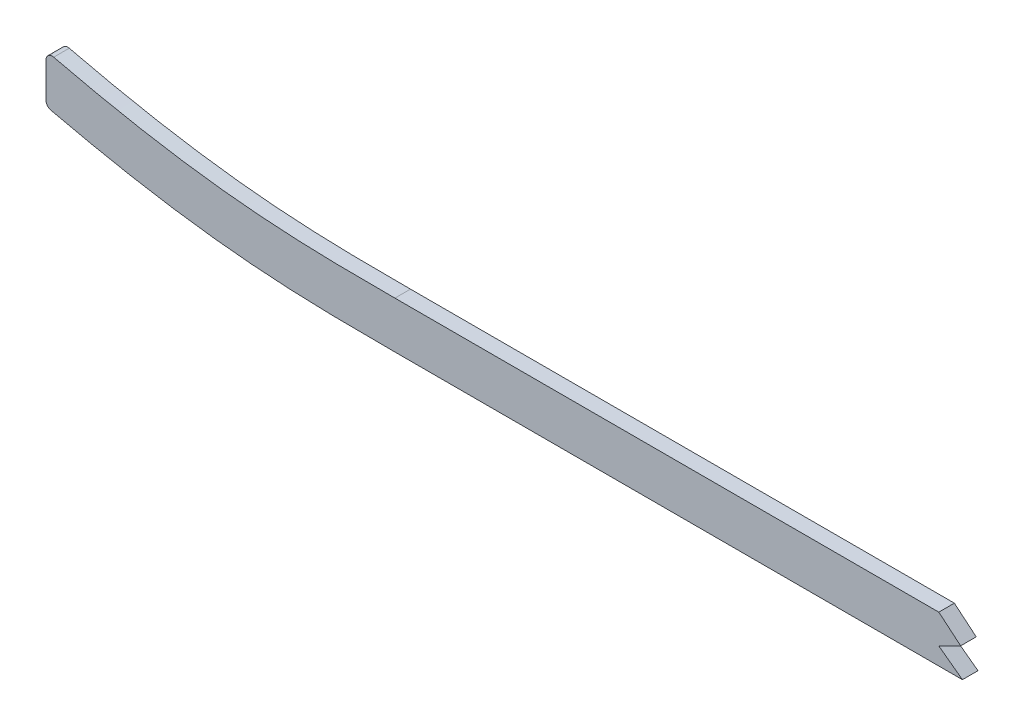
SolidWorks part; units mm, degrees
ref_plane "Front Plane" through (0, 0, 0) normal (0, 0, 1) x (1, 0, 0)
ref_plane "Top Plane" through (0, 0, 0) normal (0, 1, 0) x (1, 0, 0)
ref_plane "Right Plane" through (0, 0, 0) normal (1, 0, 0) x (0, 0, -1)
sketch "Sketch1" plane through (0, 0, 0) normal (0, 0, 1) x (1, 0, 0)
  line L0 (1046.2855, 53.4707) -> (499.61, 53.4707) construction
  line L1 (55, 0) -> (-55, 0) construction
  line L2 (1046.2855, -53.4707) -> (499.61, -53.4707)
  line L3 (1046.2855, -34.4207) -> (499.61, -34.4207)
  line L4 (99.06, -18.1493) -> (99.06, -37.7415)
  line L5 (2669.54, 9.5231) -> (2669.54, -9.569)
  spline S0 degree 5 poles (2699.7923, 7.5245) (2639.6368, 11.6572) (2579.4813, 15.4358) (2518.4981, 19.1485) (2436.3555, 23.2524) (2354.213, 26.6315) (2332.5703, 27.481) (2156.2686, 34.3778) (1979.9669, 41.6286) (1824.1143, 52.7713) (1636.9286, 53.5796) (1449.7429, 53.454) (1418.0067, 53.4707) (1324.8993, 53.4707) (1231.7919, 53.4707) (1170.4413, 53.4707) (1108.7841, 53.4707) (1047.1269, 53.4707) (1046.8464, 53.4707) (1046.5659, 53.4707) (1046.2855, 53.4707) knots 100.654805 100.654805 100.654805 100.654805 100.654805 100.654805 130.927897 130.927897 130.927897 141.337055 141.337055 141.337055 218.101815 218.101815 218.101815 233.772059 233.772059 233.772059 264.077723 264.077723 264.077723 264.216209 264.216209 264.216209 264.216209 264.216209 264.216209 weights 1 1 1 1 1 1 1 1 1 1 1 1 1 1 1 1 1 1 1 1 1 construction
  spline S1 degree 5 poles (499.61, 53.4707) (492.1368, 53.4707) (484.7543, 53.4707) (477.443, 53.4707) (448.5166, 53.4707) (419.5901, 53.4707) (398.3681, 53.4707) (355.6475, 53.4707) (312.927, 53.4707) (289.2351, 53.4703) (265.365, 53.4707) (241.4948, 53.4707) (241.4716, 53.4707) (241.4484, 53.4707) (241.4251, 53.4707) knots 19.90683 19.90683 19.90683 19.90683 19.90683 19.90683 23.637897 23.637897 23.637897 34.276546 34.276546 34.276546 46.401341 46.401341 46.401341 46.413154 46.413154 46.413154 46.413154 46.413154 46.413154 weights 1 1 1 1 1 1 1 1 1 1 1 1 1 1 1 construction
  spline S2 degree 5 poles (241.4251, 53.4707) (224.2869, 53.4707) (207.1495, 53.4673) (190.2039, 52.6866) (151.6561, 49.0319) (113.1083, 41.5037) (91.9499, 36.3426) (71.313, 30.9696) (50.6762, 24.7565) knots 0 0 0 0 0 0 8.713816 8.713816 8.713816 19.90683 19.90683 19.90683 19.90683 19.90683 19.90683 weights 1 1 1 1 1 1 1 1 1 construction
  spline S3 degree 5 poles (241.4251, -53.4707) (224.2869, -53.4707) (207.1495, -53.4673) (190.2039, -52.6866) (151.6561, -49.0319) (113.1083, -41.5037) (91.9499, -36.3426) (71.313, -30.9696) (50.6762, -24.7565) knots 0 0 0 0 0 0 8.713816 8.713816 8.713816 19.90683 19.90683 19.90683 19.90683 19.90683 19.90683 weights 1 1 1 1 1 1 1 1 1
  spline S4 degree 5 poles (499.61, -53.4707) (492.1368, -53.4707) (484.7543, -53.4707) (477.443, -53.4707) (448.5166, -53.4707) (419.5901, -53.4707) (398.3681, -53.4707) (355.6475, -53.4707) (312.927, -53.4707) (289.2351, -53.4703) (265.365, -53.4707) (241.4948, -53.4707) (241.4716, -53.4707) (241.4484, -53.4707) (241.4251, -53.4707) knots 19.90683 19.90683 19.90683 19.90683 19.90683 19.90683 23.637897 23.637897 23.637897 34.276546 34.276546 34.276546 46.401341 46.401341 46.401341 46.413154 46.413154 46.413154 46.413154 46.413154 46.413154 weights 1 1 1 1 1 1 1 1 1 1 1 1 1 1 1
  spline S5 degree 5 poles (2699.7923, -7.5245) (2639.6368, -11.6572) (2579.4813, -15.4358) (2518.4981, -19.1485) (2436.3555, -23.2524) (2354.213, -26.6315) (2332.5703, -27.481) (2156.2686, -34.3778) (1979.9669, -41.6286) (1824.1143, -52.7713) (1636.9286, -53.5796) (1449.7429, -53.454) (1418.0067, -53.4707) (1324.8993, -53.4707) (1231.7919, -53.4707) (1170.4413, -53.4707) (1108.7841, -53.4707) (1047.1269, -53.4707) (1046.8464, -53.4707) (1046.5659, -53.4707) (1046.2855, -53.4707) knots 100.654805 100.654805 100.654805 100.654805 100.654805 100.654805 130.927897 130.927897 130.927897 141.337055 141.337055 141.337055 218.101815 218.101815 218.101815 233.772059 233.772059 233.772059 264.077723 264.077723 264.077723 264.216209 264.216209 264.216209 264.216209 264.216209 264.216209 weights 1 1 1 1 1 1 1 1 1 1 1 1 1 1 1 1 1 1 1 1 1
  spline S6 degree 1 poles (2698.4867, 11.4807) (1046.2855, -34.4207) knots 0 0 1 1 construction
  spline S7 degree 1 poles (499.61, -34.4207) (241.4252, -34.4207) knots 0 0 1 1 construction
  spline S8 degree 1 poles (241.4252, -34.4207) (56.168, -6.5153) knots 0 0 1 1 construction
  spline S9 degree 3 poles (2698.4867, 11.4807) (2691.2474, 10.9833) (2679.1952, 10.1655) (2662.2765, 9.0388) (2635.6663, 7.2925) (2596.8577, 4.8261) (2545.7297, 1.7583) (2494.4053, -1.0986) (2451.533, -3.2666) (2417.1983, -4.8671) (2391.4571, -6.0036) (2365.6347, -7.0869) (2339.5463, -8.1377) (2313.4661, -9.1651) (2287.6124, -10.1795) (2261.7633, -11.201) (2227.2853, -12.5838) (2184.1756, -14.3661) (2132.4291, -16.6074) (2063.4255, -19.7089) (1977.1749, -23.7005) (1873.7325, -28.1494) (1770.3746, -31.6575) (1667.0857, -33.7931) (1581.0111, -34.3832) (1512.074, -34.4278) (1443.0615, -34.4095) (1356.8009, -34.4244) (1218.7946, -34.4185) (1115.289, -34.4207) (1046.2855, -34.4207) knots 100.654805 100.654805 100.654805 100.654805 102.842388 104.300777 105.766098 110.877392 115.988686 121.09998 126.211274 128.766921 131.322568 133.878215 136.433862 138.989509 141.545156 144.100803 146.656449 151.767743 156.879037 161.990331 172.212919 182.435507 192.658094 202.880682 213.10327 218.214564 223.325858 233.548445 243.771033 264.216209 264.216209 264.216209 264.216209
  spline S10 degree 3 poles (499.61, -34.4207) (488.6147, -34.4207) (472.2364, -34.4207) (449.9402, -34.4207) (427.7713, -34.4207) (405.8747, -34.4207) (384.5849, -34.4207) (368.9002, -34.4207) (353.3766, -34.4207) (332.6085, -34.4207) (306.2878, -34.4206) (274.0235, -34.4205) (252.271, -34.4207) (241.4252, -34.4207) knots 19.90683 19.90683 19.90683 19.90683 23.22012 24.876765 26.533411 29.846701 31.503346 33.159992 34.816637 36.473282 39.786573 43.099863 46.413154 46.413154 46.413154 46.413154
  spline S11 degree 3 poles (241.4252, -34.4207) (239.3949, -34.4207) (235.3223, -34.4205) (227.2744, -34.3987) (217.3194, -34.2975) (205.5307, -33.9764) (189.9633, -33.2126) (170.697, -31.5435) (147.5333, -28.3144) (125.4828, -24.2021) (107.4399, -20.1965) (92.2061, -16.4882) (75.9505, -12.2555) (63.6202, -8.7589) (56.168, -6.5153) knots 0 0 0 0 0.622088 1.244177 2.488354 3.732531 4.976707 7.465061 9.953415 12.441768 14.558235 15.802412 17.418476 19.90683 19.90683 19.90683 19.90683
  point P2 (0, 0)
  dimension "D1" = 50.6762
  dimension "D3" = 99.06
  dimension "D4" = 2669.54
  dimension "D2" = 19.05
extrude "Boss-Extrude1" add sketch "Sketch1" along normal mid plane 6.35 contours S10 S11 L4 S3 S4 L2 S5 L5 S9 L3
sketch "Sketch2" plane through (0, 0, 3.175) normal (0, 0, 1) x (1, 0, 0)
  line L0 (2187.01, -14.2633) -> (2312.9875, -14.2633)
  line L1 (2312.9875, -14.2633) -> (2312.9875, -9.1833)
  spline S0 degree 3 poles (689.0175, 232.3189) (4033.8285, 148.9311) (3356.6623, 54.6077) (2635.6663, 7.2925) (2596.8577, 4.8261) (2545.7297, 1.7583) (2494.4053, -1.0986) (2451.533, -3.2666) (2417.1983, -4.8671) (2391.4571, -6.0036) (2365.6347, -7.0869) (2339.5463, -8.1377) (2313.4661, -9.1651) (2287.6124, -10.1795) (2261.7633, -11.201) (2227.2853, -12.5838) (2184.1756, -14.3661) (2132.4291, -16.6074) (2063.4255, -19.7089) (1977.1749, -23.7005) (1873.7325, -28.1494) (1770.3746, -31.6575) (1667.0857, -33.7931) (1581.0111, -34.3832) (1512.074, -34.4278) (1443.0615, -34.4095) (1356.8009, -34.4244) (551.9641, -34.3896) (-218.4198, -34.7282) (-953.6342, -29.9632) knots -106.828462 -106.828462 -106.828462 -106.828462 104.300777 105.766098 110.877392 115.988686 121.09998 126.211274 128.766921 131.322568 133.878215 136.433862 138.989509 141.545156 144.100803 146.656449 151.767743 156.879037 161.990331 172.212919 182.435507 192.658094 202.880682 213.10327 218.214564 223.325858 233.548445 243.771033 461.793666 461.793666 461.793666 461.793666 only from (2669.54, 9.5231) to (1046.2855, -34.4207) construction
  spline S1 degree 3 poles (2669.54, 9.5231) (2667.1265, 9.3624) (2659.8616, 8.8803) (2635.6663, 7.2925) (2596.8577, 4.8261) (2545.7297, 1.7583) (2494.4053, -1.0986) (2451.533, -3.2666) (2417.1983, -4.8671) (2391.4571, -6.0036) (2365.6347, -7.0869) (2339.5463, -8.1377) (2313.4661, -9.1651) (2287.6124, -10.1795) (2261.7633, -11.201) (2227.2853, -12.5838) (2184.1756, -14.3661) (2132.4291, -16.6074) (2063.4255, -19.7089) (1977.1749, -23.7005) (1873.7325, -28.1494) (1770.3746, -31.6575) (1667.0857, -33.7931) (1581.0111, -34.3832) (1512.074, -34.4278) (1443.0615, -34.4095) (1356.8009, -34.4244) (1218.7946, -34.4185) (1115.289, -34.4207) (1046.2855, -34.4207) knots 103.571583 103.571583 103.571583 103.571583 104.300777 105.766098 110.877392 115.988686 121.09998 126.211274 128.766921 131.322568 133.878215 136.433862 138.989509 141.545156 144.100803 146.656449 151.767743 156.879037 161.990331 172.212919 182.435507 192.658094 202.880682 213.10327 218.214564 223.325858 233.548445 243.771033 264.216209 264.216209 264.216209 264.216209
  point P2 (0, 0)
  spline M9 degree 3 poles (2698.4867, 11.4807) (2691.2474, 10.9833) (2679.1952, 10.1655) (2662.2765, 9.0388) (2635.6663, 7.2925) (2596.8577, 4.8261) (2545.7297, 1.7583) (2494.4053, -1.0986) (2451.533, -3.2666) (2417.1983, -4.8671) (2391.4571, -6.0036) (2365.6347, -7.0869) (2339.5463, -8.1377) (2313.4661, -9.1651) (2287.6124, -10.1795) (2261.7633, -11.201) (2227.2853, -12.5838) (2184.1756, -14.3661) (2132.4291, -16.6074) (2063.4255, -19.7089) (1977.1749, -23.7005) (1873.7325, -28.1494) (1770.3746, -31.6575) (1667.0857, -33.7931) (1581.0111, -34.3832) (1512.074, -34.4278) (1443.0615, -34.4095) (1356.8009, -34.4244) (1218.7946, -34.4185) (1115.289, -34.4207) (1046.2855, -34.4207) knots 100.654805 100.654805 100.654805 100.654805 102.842388 104.300777 105.766098 110.877392 115.988686 121.09998 126.211274 128.766921 131.322568 133.878215 136.433862 138.989509 141.545156 144.100803 146.656449 151.767743 156.879037 161.990331 172.212919 182.435507 192.658094 202.880682 213.10327 218.214564 223.325858 233.548445 243.771033 264.216209 264.216209 264.216209 264.216209 only from (2669.54, 9.5231) to (1046.2855, -34.4207)
  dimension "D1" = 2312.9875
  dimension "D2" = 5.08
extrude "Cut-Extrude1" cut sketch "Sketch2" against normal through all contours L0 L1 M9
fillet "Fillet1" radius 2.54 6 edges at (2669.54, -9.569, 0) (2669.54, 9.5231, 0) (99.06, -37.7415, 0) (99.06, -18.1493, 0) (2312.9875, -14.2633, 0)
sketch "Sketch3" plane through (0, 0, 3.175) normal (0, 0, 1) x (1, 0, 0)
  line L0 (463.3586, -34.4207) -> (472.2717, -41.8744)
  line L10 (472.2717, -41.8744) -> (463.3586, -46.3842)
  line L11 (463.3586, -46.3842) -> (472.9974, -53.4707)
  line L28 (463.3586, -34.4207) -> (463.3586, 321.4412)
  line L29 (463.3586, 321.4412) -> (2811.1683, 250.9103)
  line L30 (2811.1683, 250.9103) -> (2795.5242, -269.845)
  line L31 (2795.5242, -269.845) -> (510.0958, -269.845)
  line L32 (510.0958, -269.845) -> (472.9974, -53.4707)
  spline S0 degree 3 poles (499.61, -34.4207) (488.6147, -34.4207) (472.2364, -34.4207) (449.9402, -34.4207) (427.7713, -34.4207) (405.8747, -34.4207) (384.5849, -34.4207) (368.9002, -34.4207) (353.3766, -34.4207) (332.6085, -34.4207) (306.2878, -34.4206) (274.0235, -34.4205) (252.271, -34.4207) (241.4252, -34.4207) knots 19.90683 19.90683 19.90683 19.90683 23.22012 24.876765 26.533411 29.846701 31.503346 33.159992 34.816637 36.473282 39.786573 43.099863 46.413154 46.413154 46.413154 46.413154 construction
  spline S1 degree 5 poles (499.61, -53.4707) (492.1368, -53.4707) (484.7543, -53.4707) (477.443, -53.4707) (448.5166, -53.4707) (419.5901, -53.4707) (398.3681, -53.4707) (355.6475, -53.4707) (312.927, -53.4707) (289.2351, -53.4703) (265.365, -53.4707) (241.4948, -53.4707) (241.4716, -53.4707) (241.4484, -53.4707) (241.4251, -53.4707) knots 19.90683 19.90683 19.90683 19.90683 19.90683 19.90683 23.637897 23.637897 23.637897 34.276546 34.276546 34.276546 46.401341 46.401341 46.401341 46.413154 46.413154 46.413154 46.413154 46.413154 46.413154 weights 1 1 1 1 1 1 1 1 1 1 1 1 1 1 1 construction
extrude "Cut-Extrude2" cut sketch "Sketch3" against normal blind 7.62 contours L31 L32 L11 L10 L0 L28 L29 L30
